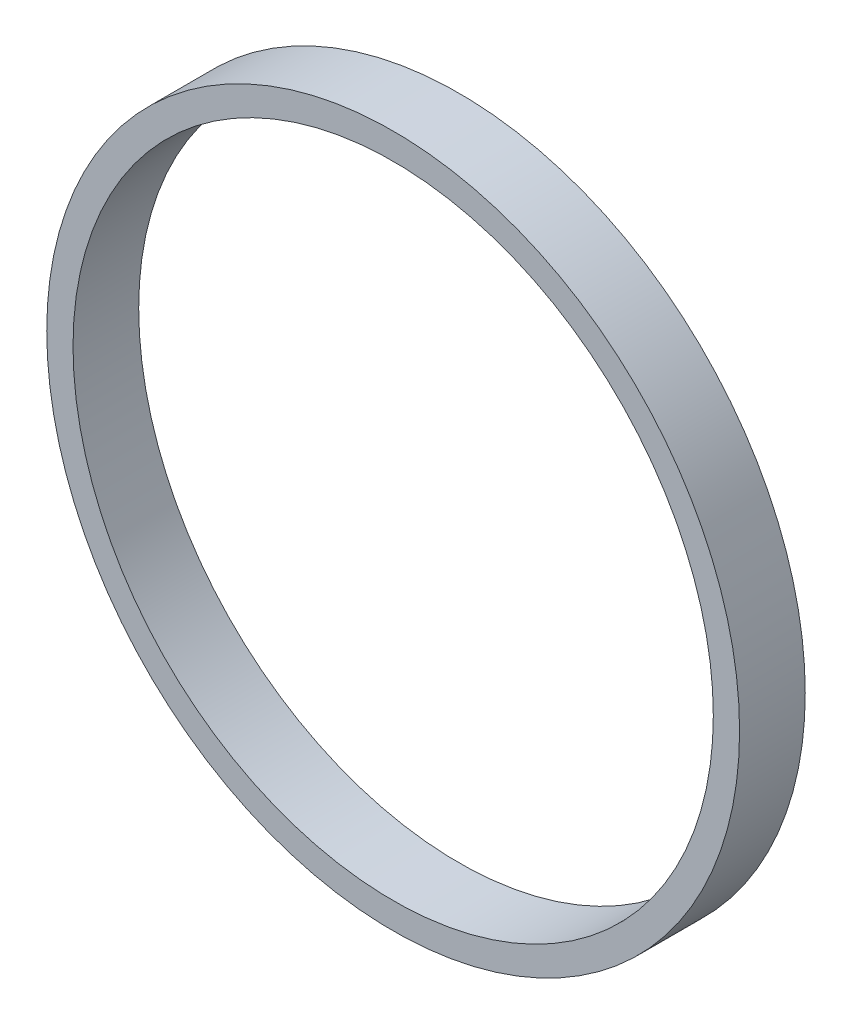
SolidWorks part; units mm, degrees
ref_plane "Front Plane" through (0, 0, 0) normal (0, 0, 1) x (1, 0, 0)
ref_plane "Top Plane" through (0, 0, 0) normal (0, 1, 0) x (1, 0, 0)
ref_plane "Right Plane" through (0, 0, 0) normal (1, 0, 0) x (0, 0, -1)
sketch "Sketch1" plane through (0, 0, 0) normal (0, 0, 1) x (1, 0, 0)
  circle A0 centre (0, 0) radius 48.75
  dimension "D1" = 97.5
extrude "Extrude-Thin1" add sketch "Sketch1" along normal blind 10 thin
